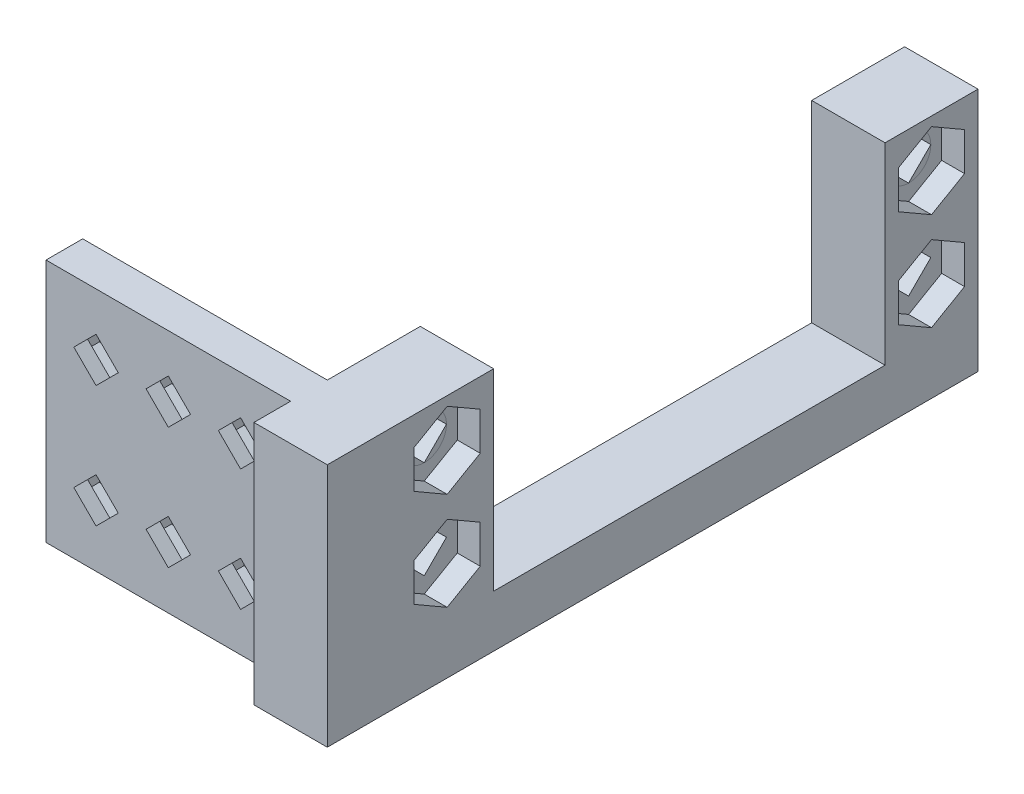
SolidWorks part; units mm, degrees
material "ABS"
ref_plane "Front Plane" through (0, 0, 0) normal (0, 0, 1) x (1, 0, 0)
ref_plane "Top Plane" through (0, 0, 0) normal (0, 1, 0) x (1, 0, 0)
ref_plane "Right Plane" through (0, 0, 0) normal (1, 0, 0) x (0, 0, -1)
sketch "Sketch1" plane through (0, 0, 0) normal (0, 1, 0) x (1, 0, 0)
  line L0 (0, 59.944) -> (0, 0)
  line L1 (0, 0) -> (-25.4, 0)
  line L2 (-25.4, 0) -> (-25.4, -7.62)
  line L3 (-25.4, -7.62) -> (7.62, -7.62)
  line L4 (7.62, -7.62) -> (7.62, 59.944)
  line L5 (7.62, 59.944) -> (0, 59.944)
  line L6 (0, 50.292) -> (7.62, 50.292) construction
  line L7 (7.62, 50.292) -> (0, 9.652) construction
  line L8 (0, 9.652) -> (7.62, 9.652) construction
  dimension "D1" = 25.4
  dimension "D2" = 40.64
  dimension "D3" = 7.62
  dimension "D4" = 7.62
  dimension "D5" = 9.652
  dimension "D6" = 9.652
extrude "Boss-Extrude1" add sketch "Sketch1" along normal mid plane 25.4
sketch "Sketch2" plane through (0, 12.7, 0) normal (0, 1, 0) x (1, 0, 0)
  line L0 (0, 59.944) -> (0, 0) construction
  line L1 (0, 50.292) -> (7.62, 50.292)
  line L2 (0, 50.292) -> (0, 9.652)
  line L3 (0, 9.652) -> (7.62, 9.652)
  line L4 (7.62, 50.292) -> (7.62, 9.652)
  line L5 (7.62, -7.62) -> (7.62, 59.944) construction
  line L6 (0, 9.652) -> (7.62, 9.652) construction
  dimension "D1" = 40.64
extrude "Cut-Extrude1" cut sketch "Sketch2" against normal blind 20
sketch "Sketch3" plane through (7.62, 0, 0) normal (1, 0, 0) x (0, 0, -1)
  line L0 (29.972, -7.3) -> (29.972, -12.7) construction
  line L1 (9.652, -7.3) -> (50.292, -7.3) construction
  line L2 (-7.62, -12.7) -> (59.944, -12.7) construction
  line L3 (9.652, 2.7) -> (50.292, 2.7) construction
  line L5 (59.944, 12.7) -> (59.944, -12.7) construction
  line L6 (55.118, 10.0879) -> (52.8101, 7.78)
  line L7 (55.118, 10.0879) -> (57.4259, 7.78)
  line L8 (52.8101, 7.78) -> (55.118, 5.4721)
  line L9 (57.4259, 7.78) -> (55.118, 5.4721)
  line L10 (55.118, 10.0879) -> (55.118, 5.4721) construction
  line L11 (52.8101, 7.78) -> (57.4259, 7.78) construction
  line L12 (7.1339, 7.78) -> (2.5181, 7.78) construction
  line L13 (4.826, 10.0879) -> (4.826, 5.4721) construction
  line L14 (2.5181, 7.78) -> (4.826, 5.4721)
  line L15 (7.1339, 7.78) -> (4.826, 5.4721)
  line L16 (4.826, 10.0879) -> (2.5181, 7.78)
  line L17 (4.826, 10.0879) -> (7.1339, 7.78)
  line L18 (-7.62, -7.3) -> (59.944, -7.3) construction
  line L19 (-7.62, 12.7) -> (-7.62, -12.7) construction
  line L20 (9.652, -7.3) -> (9.652, 12.7) construction
  line L21 (50.292, -7.3) -> (50.292, 12.7) construction
  line L22 (55.118, 12.7) -> (55.118, -7.3) construction
  line L23 (50.292, 12.7) -> (59.944, 12.7) construction
  line L24 (52.8101, -2.38) -> (57.4259, -2.38) construction
  line L25 (55.118, -4.6879) -> (55.118, -0.0721) construction
  line L26 (57.4259, -2.38) -> (55.118, -0.0721)
  line L27 (52.8101, -2.38) -> (55.118, -0.0721)
  line L28 (55.118, -4.6879) -> (57.4259, -2.38)
  line L29 (55.118, -4.6879) -> (52.8101, -2.38)
  line L30 (4.826, -4.6879) -> (4.826, -0.0721) construction
  line L31 (7.1339, -2.38) -> (2.5181, -2.38) construction
  line L32 (4.826, -4.6879) -> (7.1339, -2.38)
  line L33 (4.826, -4.6879) -> (2.5181, -2.38)
  line L34 (7.1339, -2.38) -> (4.826, -0.0721)
  line L35 (2.5181, -2.38) -> (4.826, -0.0721)
  circle A0 centre (55.118, 7.78) radius 1.6319 construction
  circle A1 centre (4.826, 7.78) radius 1.6319 construction
  circle A2 centre (55.118, -2.38) radius 1.6319 construction
  circle A3 centre (4.826, -2.38) radius 1.6319 construction
  dimension "D1" = 3.2639
  dimension "D2" = 5.08
extrude "Cut-Extrude2" cut sketch "Sketch3" against normal through all
sketch "Sketch12" plane through (7.62, 0, 0) normal (1, 0, 0) x (0, 0, -1)
  line L0 (52.8101, -2.38) -> (57.4259, -2.38) construction
  line L1 (8.255, 9.7597) -> (4.826, 11.7395)
  line L2 (4.826, 11.7395) -> (1.397, 9.7597)
  line L3 (1.397, 9.7597) -> (1.397, 5.8003)
  line L4 (1.397, 5.8003) -> (4.826, 3.8205)
  line L5 (4.826, 3.8205) -> (8.255, 5.8003)
  line L6 (8.255, 5.8003) -> (8.255, 9.7597)
  line L7 (4.826, 1.5795) -> (1.397, -0.4003)
  line L8 (1.397, -0.4003) -> (1.397, -4.3597)
  line L9 (1.397, -4.3597) -> (4.826, -6.3395)
  line L10 (4.826, -6.3395) -> (8.255, -4.3597)
  line L11 (8.255, -4.3597) -> (8.255, -0.4003)
  line L12 (8.255, -0.4003) -> (4.826, 1.5795)
  line L13 (55.118, 1.5795) -> (51.689, -0.4003)
  line L14 (51.689, -0.4003) -> (51.689, -4.3597)
  line L15 (51.689, -4.3597) -> (55.118, -6.3395)
  line L16 (55.118, -6.3395) -> (58.547, -4.3597)
  line L17 (58.547, -4.3597) -> (58.547, -0.4003)
  line L18 (58.547, -0.4003) -> (55.118, 1.5795)
  line L20 (55.118, 11.7395) -> (51.689, 9.7597)
  line L21 (51.689, 9.7597) -> (51.689, 5.8003)
  line L22 (51.689, 5.8003) -> (55.118, 3.8205)
  line L23 (55.118, 3.8205) -> (58.547, 5.8003)
  line L24 (58.547, 5.8003) -> (58.547, 9.7597)
  line L25 (58.547, 9.7597) -> (55.118, 11.7395)
  circle A0 centre (4.826, 7.78) radius 3.429 construction
  circle A1 centre (4.826, -2.38) radius 3.429 construction
  circle A2 centre (55.118, -2.38) radius 3.429 construction
  circle A3 centre (55.118, 7.78) radius 3.429 construction
  dimension "D1" = 6.858
extrude "Cut-Extrude6" cut sketch "Sketch12" against normal blind 2.3813
sketch "Sketch4" plane through (7.62, 0, 0) normal (1, 0, 0) x (0, 0, -1)
  circle A0 centre (4.826, 7.78) radius 2.3079
  circle A1 centre (55.118, 7.78) radius 2.3079
  circle A2 centre (4.826, 7.78) radius 1.6319 construction
  circle A3 centre (55.118, 7.78) radius 1.6319 construction
split line "Split Line1"
sketch "Sketch9" plane through (0, 0, 0) normal (0, 0, -1) x (-1, 0, 0)
  line L0 (12.7, 12.7) -> (12.7, -0.0721) construction
  line L1 (0, 12.7) -> (25.4, 12.7) construction
  line L2 (0, 6.314) -> (2.8881, 6.314) construction
  line L3 (5.196, 4.006) -> (7.504, 6.314)
  line L4 (7.504, 6.314) -> (5.196, 8.6219)
  line L5 (5.196, 8.6219) -> (2.8881, 6.314)
  line L6 (2.8881, 6.314) -> (5.196, 4.006)
  line L7 (20.204, 4.006) -> (22.5119, 6.314)
  line L8 (22.5119, 6.314) -> (20.204, 8.6219)
  line L9 (20.204, 8.6219) -> (17.896, 6.314)
  line L11 (17.896, 6.314) -> (20.204, 4.006)
  line L12 (0, 12.7) -> (0, -12.7) construction
  line L13 (7.504, 6.314) -> (10.3921, 6.314) construction
  line L14 (15.0079, 6.314) -> (17.896, 6.314) construction
  line L15 (22.5119, 6.314) -> (25.4, 6.314) construction
  line L18 (0, -0.0721) -> (25.4, -0.0721) construction
  line L20 (25.4, 12.7) -> (25.4, -12.7) construction
  line L44 (12.7, 4.006) -> (15.0079, 6.314)
  line L45 (15.0079, 6.314) -> (12.7, 8.6219)
  line L46 (12.7, 8.6219) -> (10.3921, 6.314)
  line L47 (10.3921, 6.314) -> (12.7, 4.006)
  circle A0 centre (5.196, 6.314) radius 1.632 construction
  circle A1 centre (20.204, 6.314) radius 1.632 construction
  circle A6 centre (12.7, 6.314) radius 1.6319 construction
  dimension "D2" = 3.2639
extrude "Cut-Extrude5" cut sketch "Sketch9" against normal through all
sketch "Sketch13" plane through (0, 0, 0) normal (0, 0, -1) x (-1, 0, 0)
  line L1 (8.625, 4.3342) -> (8.625, 8.2937)
  line L2 (8.625, 8.2937) -> (5.196, 10.2734)
  line L3 (5.196, 10.2734) -> (1.767, 8.2937)
  line L4 (1.767, 8.2937) -> (1.767, 4.3342)
  line L5 (1.767, 4.3342) -> (5.196, 2.3545)
  line L6 (5.196, 2.3545) -> (8.625, 4.3342)
  line L7 (12.7, 2.3545) -> (16.129, 4.3342)
  line L8 (16.129, 4.3342) -> (16.129, 8.2937)
  line L9 (16.129, 8.2937) -> (12.7, 10.2734)
  line L10 (12.7, 10.2734) -> (9.271, 8.2937)
  line L11 (9.271, 8.2937) -> (9.271, 4.3342)
  line L12 (9.271, 4.3342) -> (12.7, 2.3545)
  line L14 (20.204, 2.3545) -> (23.633, 4.3342)
  line L15 (23.633, 4.3342) -> (23.633, 8.2937)
  line L16 (23.633, 8.2937) -> (20.204, 10.2734)
  line L17 (20.204, 10.2734) -> (16.775, 8.2937)
  line L18 (16.775, 8.2937) -> (16.775, 4.3342)
  line L19 (16.775, 4.3342) -> (20.204, 2.3545)
  circle A0 centre (5.196, 6.314) radius 3.429 construction
  circle A1 centre (12.7, 6.314) radius 3.429 construction
  circle A2 centre (20.204, 6.314) radius 3.429 construction
  dimension "D1" = 6.858
extrude "Cut-Extrude7" cut sketch "Sketch13" against normal blind 2.3813
mirror "Mirror2" about plane through (0, 0, 0) normal (0, 1, 0) of "Cut-Extrude7", "Cut-Extrude5"
sketch "Sketch14" plane through (0, 12.7, 0) normal (0, 1, 0) x (1, 0, 0)
  line L0 (-25.4, -3.81) -> (0, -3.81)
  line L1 (-25.4, 0) -> (-25.4, -7.62) construction
  line L2 (0, -3.81) -> (0, -7.62)
  line L3 (-25.4, -7.62) -> (7.62, -7.62) construction
  line L4 (-25.4, -3.81) -> (-25.4, -7.62)
  line L5 (-25.4, -7.62) -> (0, -7.62)
extrude "Cut-Extrude8" cut sketch "Sketch14" against normal through all
sketch "Sketch15" plane through (0, 0, 0) normal (0, 0, -1) x (-1, 0, 0)
  line L0 (0, 12.7) -> (25.4, 12.7) construction
  line L1 (25.4, -12.7) -> (22.606, -12.7)
  line L2 (25.4, -12.7) -> (25.4, 12.7)
  line L3 (25.4, 12.7) -> (22.606, 12.7)
  line L4 (22.606, -12.7) -> (22.606, 12.7)
  dimension "D1" = 2.794
extrude "Cut-Extrude9" [suppressed] cut sketch "Sketch15" against normal through all
